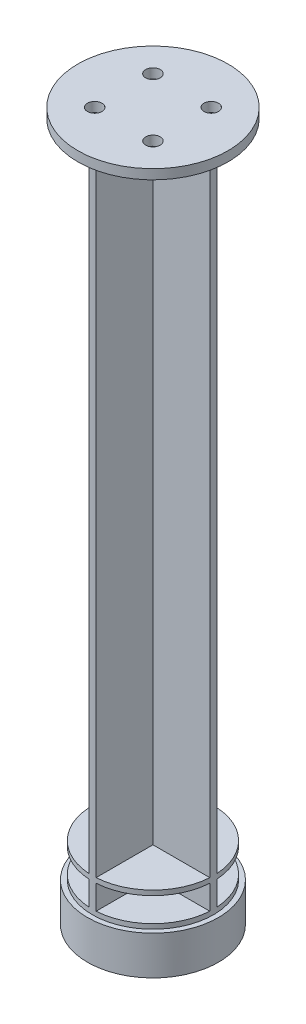
SolidWorks part; units mm, degrees
material "PE High Density"
ref_plane "Front Plane" through (0, 0, 0) normal (0, 0, 1) x (1, 0, 0)
ref_plane "Top Plane" through (0, 0, 0) normal (0, 1, 0) x (1, 0, 0)
ref_plane "Right Plane" through (0, 0, 0) normal (1, 0, 0) x (0, 0, -1)
sketch "Sketch1" plane through (0, 0, 0) normal (0, 1, 0) x (1, 0, 0)
  circle A0 centre (0, 0) radius 13.5
  dimension "D1" = 27
extrude "Boss-Extrude1" add sketch "Sketch1" along normal blind 8
sketch "Sketch3" plane through (0, 8, 0) normal (0, 1, 0) x (1, 0, 0)
  circle A0 centre (0, 0) radius 12.5
  dimension "D1" = 25
extrude "Boss-Extrude3" add sketch "Sketch3" along normal blind 1
sketch "Sketch4" plane through (0, 9, 0) normal (0, 1, 0) x (1, 0, 0)
  line L0 (-0.75, -0.75) -> (-12.4775, -0.75)
  line L5 (0.75, 0.75) -> (-0.75, -0.75) construction
  line L6 (0.75, -0.75) -> (-0.75, 0.75) construction
  line L7 (-0.75, 0.75) -> (-0.75, 12.4775)
  line L8 (-12.4775, 0.75) -> (-0.75, 0.75)
  line L10 (0.75, 12.4775) -> (0.75, 0.75)
  line L11 (0.75, 0.75) -> (12.4775, 0.75)
  line L13 (12.4775, -0.75) -> (0.75, -0.75)
  line L14 (0.75, -0.75) -> (0.75, -12.4775)
  line L16 (-0.75, -12.4775) -> (-0.75, -0.75)
  arc A0 (0.75, 12.4775) -> (-0.75, 12.4775) centre (0, 0) ccw
  arc A1 (-12.4775, 0.75) -> (-12.4775, -0.75) centre (0, 0) ccw
  arc A2 (-0.75, -12.4775) -> (0.75, -12.4775) centre (0, 0) ccw
  arc A3 (12.4775, -0.75) -> (12.4775, 0.75) centre (0, 0) ccw
  point P1 (0, 0)
  dimension "D3" = 25
  dimension "D1" = 1.5
  dimension "D2" = 1.5
  dimension "D4" = 1.5
  dimension "D5" = 1.5
  dimension "D6" = 0
extrude "Boss-Extrude4" add sketch "Sketch4" along normal blind 135
ref_plane "Plane1" through (0, 14, 0) normal (0, 1, 0) x (1, 0, 0)
sketch "Sketch5" plane through (0, 14, 0) normal (0, 1, 0) x (1, 0, 0)
  circle A0 centre (0, 0) radius 12.5
  dimension "D1" = 25
extrude "Boss-Extrude5" add sketch "Sketch5" along normal blind 1
sketch "Sketch7" plane through (0, 144, 0) normal (0, 1, 0) x (1, 0, 0)
  circle A0 centre (0, 0) radius 15.5
  dimension "D1" = 31
sketch "Sketch8" plane through (0, 0, 0) normal (0, 0, 1) x (1, 0, 0)
  line L0 (0, 0) -> (0, -7)
  line L1 (0, -7) -> (13.5, 0)
  line L2 (13.5, 0) -> (0, 0)
  dimension "D1" = 7
  dimension "D2" = 90
  dimension "D3" = 13.5
revolve "Revolve1" add sketch "Sketch8" angle 360 about L0
extrude "Boss-Extrude8" add sketch "Sketch7" along normal blind 2
sketch "Sketch9" plane through (0, 146, 0) normal (0, 1, 0) x (1, 0, 0)
  line L0 (0, 0) -> (-6.0104, 6.0104) construction
  line L1 (0, 0) -> (0, 10.5015) construction
  circle A0 centre (-6.0104, 6.0104) radius 1.5
  circle A1 centre (0, 0) radius 15.5 construction
  circle A2 centre (6.0104, 6.0104) radius 1.5
  circle A3 centre (6.0104, -6.0104) radius 1.5
  circle A4 centre (-6.0104, -6.0104) radius 1.5
  point P14 (0, 0)
  dimension "D1" = 3
  dimension "D2" = 8.5
  dimension "D3" = 45
  dimension "D4" = 4
extrude "Cut-Extrude1" cut sketch "Sketch9" against normal blind 2
